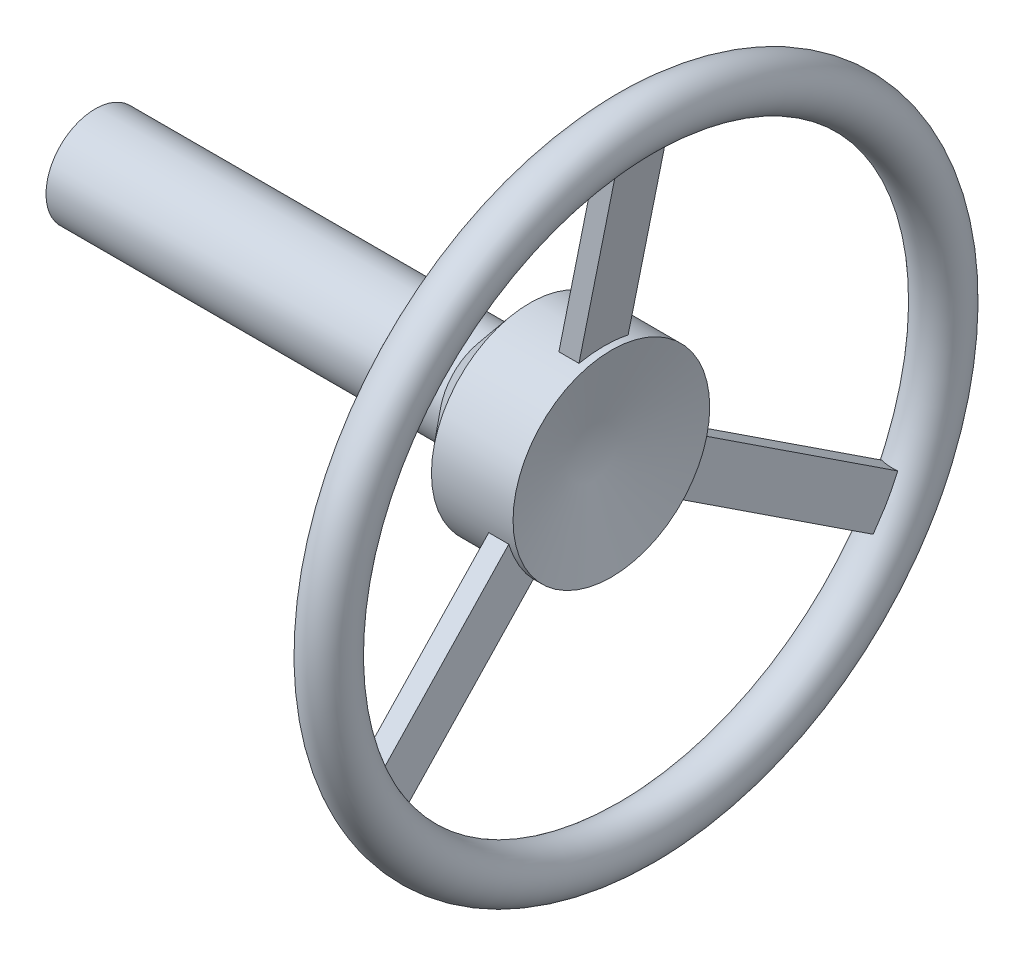
SolidWorks part; units mm, degrees
ref_plane "Front Plane" through (0, 0, 0) normal (0, 0, 1) x (1, 0, 0)
ref_plane "Top Plane" through (0, 0, 0) normal (0, 1, 0) x (1, 0, 0)
ref_plane "Right Plane" through (0, 0, 0) normal (1, 0, 0) x (0, 0, -1)
sketch "Sketch1" plane through (0, 0, 0) normal (0, 0, 1) x (1, 0, 0)
  line L0 (-73.6957, 0) -> (91.5217, 0) construction
  line L1 (-49.7628, 0) -> (-49.7628, 5)
  line L2 (-49.7628, 5) -> (-9.7628, 5)
  line L3 (-9.7628, 5) -> (-5.5673, 10)
  line L4 (-5.5673, 10) -> (2.7327, 10)
  line L5 (2.7327, 10) -> (0.2069, 0)
  line L6 (0.2069, 0) -> (-49.7628, 0)
  dimension "D1" = 40
  dimension "D2" = 130
  dimension "D3" = 8.3
  dimension "D4" = 5
  dimension "D5" = 10
  dimension "D6" = 75.825
revolve "Revolve1" add sketch "Sketch1" angle 360 about L0
sketch "Sketch2" plane through (0, 0, 0) normal (0, 0, 1) x (1, 0, 0)
  line L1 (-155.619, 0) -> (185.9825, 0) construction
  circle A0 centre (5.2372, 31.25) radius 2.5
  dimension "D1" = 55
  dimension "D2" = 5
  dimension "D3" = 31.25
revolve "Revolve2" add sketch "Sketch2" angle 360 about L1
sketch "Sketch3" plane through (0, 0, 0) normal (0, 0, 1) x (1, 0, 0)
  line L0 (1.8372, 9.2) -> (-0.2028, 9.2)
  line L1 (-0.2028, 9.2) -> (4.2172, 31.2)
  line L2 (4.2172, 31.2) -> (6.2572, 31.2)
  line L3 (6.2572, 31.2) -> (1.8372, 9.2)
  line L4 (-91.919, 0) -> (69.3504, 0) construction
  line L5 (2.7372, 31.25) -> (2.7372, -31.25) construction
  dimension "D1" = 2
  dimension "D2" = 9.2
  dimension "D3" = 0.9
  dimension "D4" = 4.42
  dimension "D5" = 22
extrude "Boss-Extrude1" add sketch "Sketch3" along normal mid plane 5
pattern_circular "CirPattern1" count 3 over 360 about axis through (0, 0, 0) along (1, 0, 0) of "Boss-Extrude1"
